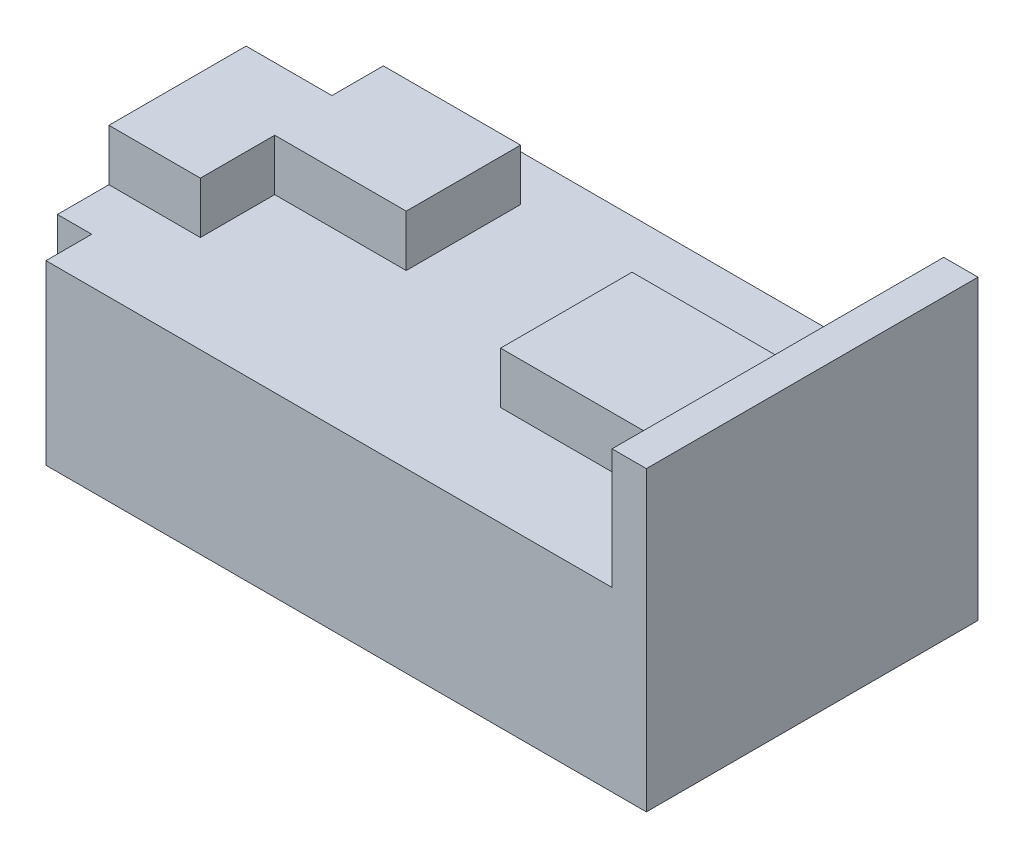
SolidWorks part; units mm, degrees
ref_plane "Front Plane" through (0, 0, 0) normal (0, 0, 1) x (1, 0, 0)
ref_plane "Top Plane" through (0, 0, 0) normal (0, 1, 0) x (1, 0, 0)
ref_plane "Right Plane" through (0, 0, 0) normal (1, 0, 0) x (0, 0, -1)
sketch "Sketch1" plane through (0, 0, 0) normal (0, 0, 1) x (1, 0, 0)
  line L0 (0, 0) -> (0, 26)
  line L1 (0, 26) -> (-3, 26)
  line L2 (-3, 26) -> (-3, 15.5)
  line L3 (-3, 15.5) -> (-55.5, 15.5)
  line L4 (-55.5, 15.5) -> (-55.5, 0)
  line L7 (-55.5, 0) -> (0, 0)
  dimension "D3" = 26
  dimension "D4" = 52.5
  dimension "D5" = 3
  dimension "D8" = 10.5
extrude "Boss-Extrude1" add sketch "Sketch1" along normal blind 29 contours L3 L4 L7 L0 L1 L2
sketch "Sketch2" plane through (0, 15.5, 0) normal (0, 1, 0) x (1, 0, 0)
  line L0 (-55.5, -29) -> (-55.5, 0) construction
  line L1 (-55.5, 0) -> (-52.5, 0)
  line L2 (-55.5, 0) -> (-55.5, -4)
  line L3 (-55.5, -4) -> (-52.5, -4)
  line L4 (-52.5, 0) -> (-52.5, -4)
  line L5 (-3, -29) -> (-55.5, -29) construction
  line L6 (-55.5, -29) -> (-52.5, -29)
  line L7 (-55.5, -29) -> (-55.5, -25)
  line L8 (-55.5, -25) -> (-52.5, -25)
  line L9 (-52.5, -29) -> (-52.5, -25)
  dimension "D1" = 4
  dimension "D2" = 3
  dimension "D3" = 3
  dimension "D4" = 4
extrude "Cut-Extrude1" cut sketch "Sketch2" against normal through all
sketch "Sketch3" plane through (0, 15.5, 0) normal (0, 1, 0) x (1, 0, 0)
  line L0 (-3, -29) -> (-3, 0) construction
  line L1 (-21.5, -20.25) -> (-3, -20.25)
  line L2 (-21.5, -20.25) -> (-21.5, -8.75)
  line L3 (-21.5, -8.75) -> (-3, -8.75)
  line L4 (-3, -20.25) -> (-3, -8.75)
  line L5 (-3, -29) -> (-52.5, -29) construction
  line L6 (-55.5, -4) -> (-52.5, -4) construction
  line L7 (-55.5, -25) -> (-55.5, -4) construction
  line L8 (-55.5, -20.5) -> (-47.5, -20.5)
  line L9 (-55.5, -20.5) -> (-55.5, -8.5)
  line L10 (-55.5, -8.5) -> (-48, -8.5)
  line L11 (-47.5, -20.5) -> (-47.5, -14)
  line L12 (-47.5, -14) -> (-36, -14)
  line L13 (-48, -8.5) -> (-48, -4)
  line L14 (-48, -4) -> (-36, -4)
  line L15 (-36, -14) -> (-36, -4)
  line L16 (-52.5, -25) -> (-55.5, -25) construction
  dimension "D1" = 11.5
  dimension "D2" = 18.5
  dimension "D3" = 8.75
  dimension "D4" = 12
  dimension "D5" = 8
  dimension "D6" = 12
  dimension "D7" = 10
  dimension "D8" = 0
  dimension "D9" = 0.5
  dimension "D10" = 4.5
extrude "Boss-Extrude4" add sketch "Sketch3" along normal blind 4.5
